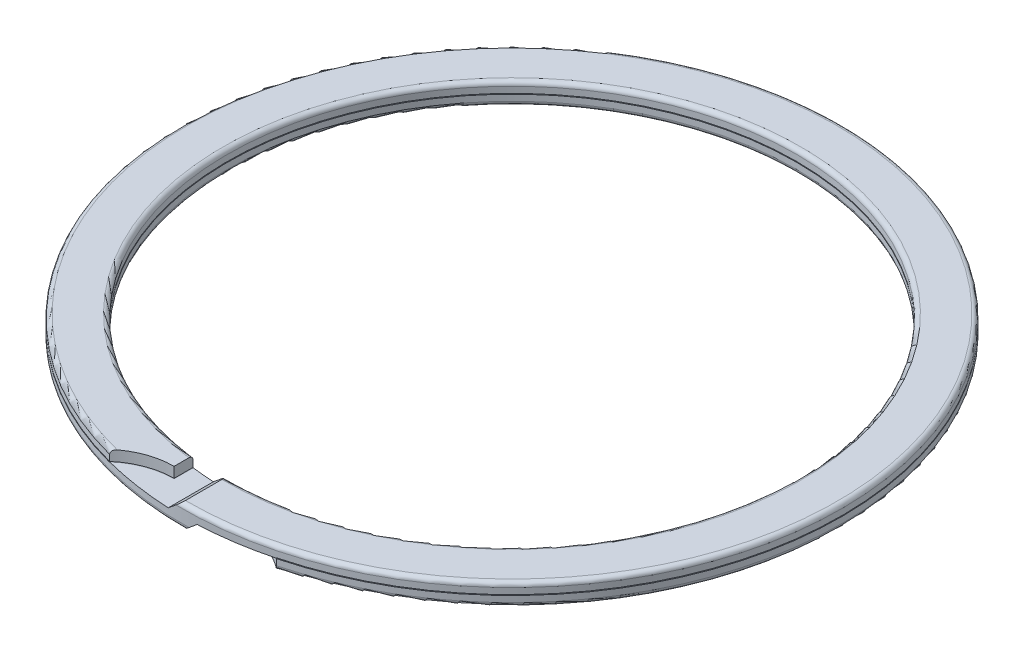
SolidWorks part; units mm, degrees
ref_plane "Front Plane" through (0, 0, 0) normal (0, 0, 1) x (1, 0, 0)
ref_plane "Top Plane" through (0, 0, 0) normal (0, 1, 0) x (1, 0, 0)
ref_plane "Right Plane" through (0, 0, 0) normal (1, 0, 0) x (0, 0, -1)
ref_plane "Plane4" through (0, 0, 0) normal (1, 0, 0) x (0, 0, -1)
sketch "Sketch1" plane through (0, 0, 0) normal (1, 0, 0) x (0, 0, -1)
  line L0 (38.2, 0.873) -> (38.2, -0.873)
  line L1 (38.782, -1.455) -> (43.668, -1.455)
  line L2 (44.25, -0.873) -> (44.25, 0.873)
  line L3 (43.668, 1.455) -> (38.782, 1.455)
  line L4 (0, -1) -> (0, 1) construction
  arc A0 (38.2, -0.873) -> (38.782, -1.455) centre (38.782, -0.873) ccw
  arc A1 (43.668, -1.455) -> (44.25, -0.873) centre (43.668, -0.873) ccw
  arc A2 (44.25, 0.873) -> (43.668, 1.455) centre (43.668, 0.873) ccw
  arc A3 (38.782, 1.455) -> (38.2, 0.873) centre (38.782, 0.873) ccw
revolve "Revolve1" add sketch "Sketch1" angle 360 about L4
ref_plane "Plane5" through (0, 0, 0) normal (0, 1, 0) x (-1, 0, 0)
sketch "Sketch2" plane through (0, 0, 0) normal (0, 1, 0) x (-1, 0, 0)
  line L0 (4.9157, 59.6052) -> (4.9157, 40.4468)
  arc A0 (4.9157, 40.4468) -> (4.9157, 59.6052) centre (4.9167, 50.026) ccw
extrude "Extrude1" cut sketch "Sketch2" along normal blind 88.5
ref_plane "Plane6" through (0, 0, 0) normal (0, 1, 0) x (-1, 0, 0)
sketch "Sketch3" plane through (0, 0, 0) normal (0, 1, 0) x (-1, 0, 0)
  line L0 (-4.9157, 40.4468) -> (-4.9157, 59.6052)
  arc A0 (-4.9157, 59.6052) -> (-4.9157, 40.4468) centre (-4.9167, 50.026) ccw
extrude "Extrude2" cut sketch "Sketch3" against normal blind 88.5
ref_plane "Plane7" through (0, 0, 0) normal (0, 0, 1) x (1, 0, 0)
sketch "Sketch4" plane through (0, 0, 0) normal (0, 0, 1) x (1, 0, 0)
  line L0 (-4.9167, 0) -> (-1.9394, 0)
  line L1 (-1.9394, 0) -> (1.94, 3.2005)
  line L2 (1.94, 3.2005) -> (-4.9167, 3.2005)
  line L3 (-4.9167, 3.2005) -> (-4.9167, 0)
extrude "Extrude3" cut sketch "Sketch4" along normal blind 88.5
ref_plane "Plane8" through (0, 0, 0) normal (0, 0, 1) x (1, 0, 0)
sketch "Sketch5" plane through (0, 0, 0) normal (0, 0, 1) x (1, 0, 0)
  line L0 (-1.94, -3.2005) -> (4.9167, -3.2005)
  line L1 (4.9167, -3.2005) -> (4.9167, 0)
  line L2 (4.9167, 0) -> (1.9394, 0)
  line L3 (1.9394, 0) -> (-1.94, -3.2005)
extrude "Extrude4" cut sketch "Sketch5" along normal blind 88.5
ref_plane "Plane9" through (0, 0, 0) normal (0, 1, 0) x (-1, 0, 0)
sketch "Sketch6" plane through (0, 0, 0) normal (0, 1, 0) x (-1, 0, 0)
  line L0 (45.135, -45.135) -> (45.135, 45.135)
  line L1 (45.135, 45.135) -> (13.1531, 45.135)
  line L2 (4.9157, 40.4468) -> (4.9157, 37.8723)
  line L3 (-4.9157, 37.8723) -> (-4.9157, 40.4468)
  line L4 (-13.1531, 45.135) -> (-45.135, 45.135)
  line L5 (-45.135, 45.135) -> (-45.135, -45.135)
  line L6 (-45.135, -45.135) -> (45.135, -45.135)
  arc A0 (13.1531, 45.135) -> (4.9157, 40.4468) centre (4.9167, 50.026) cw
  arc A1 (4.9157, 37.8723) -> (-4.9157, 37.8723) centre (0, 0) ccw
  arc A2 (-4.9157, 40.4468) -> (-13.1531, 45.135) centre (-4.9167, 50.026) cw
extrude "Extrude5" cut sketch "Sketch6" against normal blind 0.05 and the other way blind 0.05
